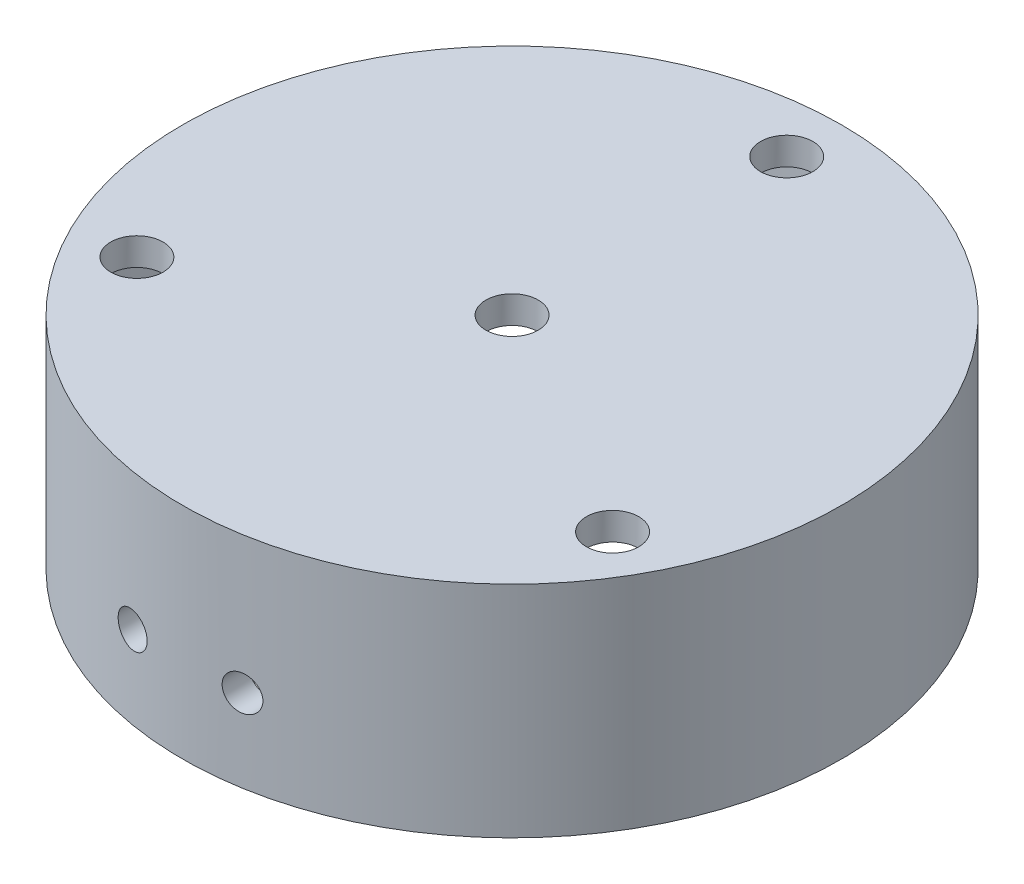
SolidWorks part; units mm, degrees
ref_plane "Alzado" through (0, 0, 0) normal (0, 0, 1) x (1, 0, 0)
ref_plane "Planta" through (0, 0, 0) normal (0, 1, 0) x (1, 0, 0)
ref_plane "Vista lateral" through (0, 0, 0) normal (1, 0, 0) x (0, 0, -1)
sketch "Croquis1" plane through (0, 0, 0) normal (0, 0, 1) x (1, 0, 0)
  line L0 (0, 0) -> (0, 127.5202) construction
  line L1 (0, 40) -> (60, 40)
  line L2 (60, 40) -> (60, 0)
  line L3 (60, 0) -> (55, 0)
  line L4 (55, 0) -> (55, 35)
  line L5 (55, 35) -> (0, 35)
  line L6 (0, 40) -> (0, 35)
  dimension "D1" = 60
  dimension "D2" = 40
  dimension "D3" = 5
  dimension "D4" = 5
revolve "Revolución1" add sketch "Croquis1" angle 360 about L0
sketch "Croquis2" plane through (0, 40, 0) normal (0, 1, 0) x (1, 0, 0)
  circle A0 centre (0, 0) radius 4.7625
  dimension "D1" = 9.525
extrude "Cortar-Extruir1" cut sketch "Croquis2" against normal through all
sketch "Croquis3" plane through (0, 0, 0) normal (0, 0, 1) x (1, 0, 0)
  circle A0 centre (-10, 15) radius 3.175
  circle A1 centre (10, 15) radius 3.175
  dimension "D1" = 6.35
  dimension "D2" = 10
  dimension "D3" = 20
  dimension "D4" = 15
extrude "Cortar-Extruir2" cut sketch "Croquis3" against normal through all both and the other way through all
sketch "Croquis4" plane through (0, 40, 0) normal (0, 1, 0) x (1, 0, 0)
  line L0 (0, 77.6577) -> (0, 0) construction
  line L1 (0, 0) -> (60.5915, -34.9825) construction
  line L2 (0, 0) -> (-60.5182, -34.9402) construction
  circle A0 centre (0, 0) radius 50
  circle A1 centre (0, 50) radius 4.7625
  circle A2 centre (0, 0) radius 60 construction
  circle A3 centre (43.3013, -25) radius 4.7625
  circle A4 centre (-43.3013, -25) radius 4.7625
  dimension "D1" = 9.525
  dimension "D4" = 10
  dimension "D2" = 120
  dimension "D3" = 120
  dimension "D5" = 3
extrude "Cortar-Extruir4" cut sketch "Croquis4" against normal through all both and the other way through all contours A0 A1 | A0 A1 | A0 A3 | A0 A3 | A0 A4 | A0 A4
